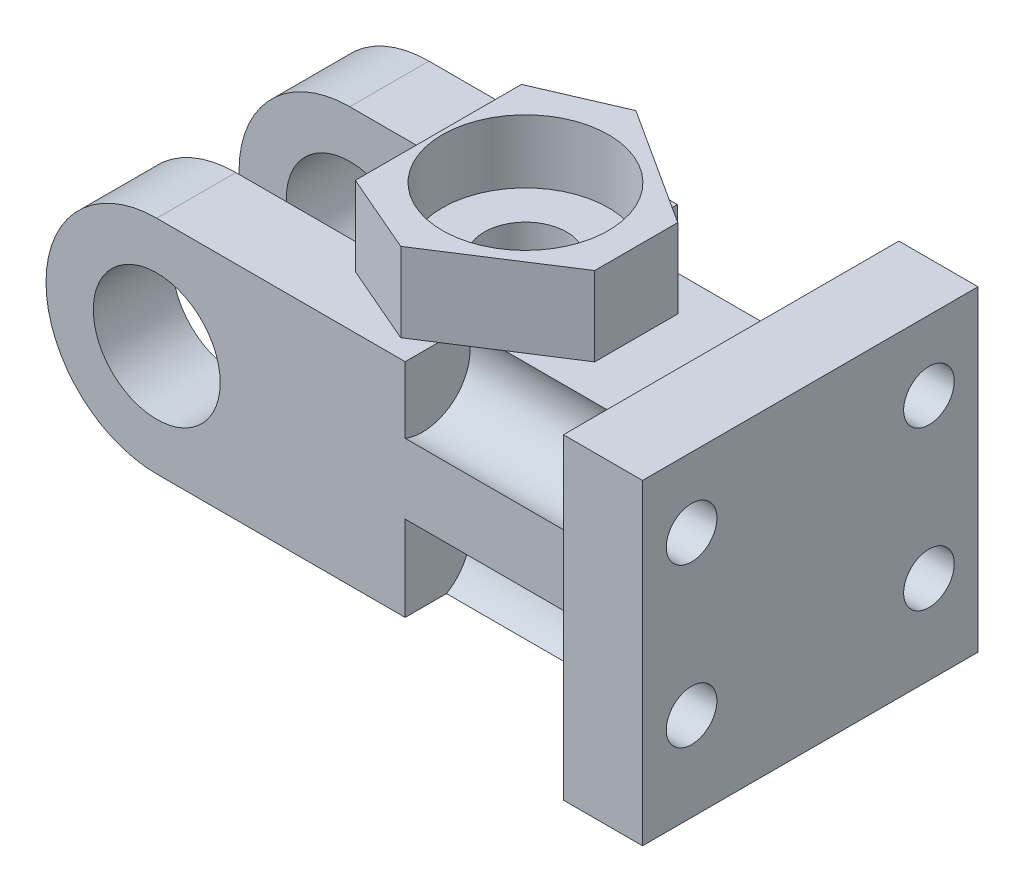
SolidWorks part; units mm, degrees
ref_plane "正面" through (0, 0, 0) normal (0, 0, 1) x (1, 0, 0)
ref_plane "平面" through (0, 0, 0) normal (0, 1, 0) x (1, 0, 0)
ref_plane "右側面" through (0, 0, 0) normal (1, 0, 0) x (0, 0, -1)
sketch "ｽｹｯﾁ1" plane through (0, 0, 0) normal (0, 0, 1) x (1, 0, 0)
  line L0 (24, 46) -> (24, 31) construction
  line L4 (24, 53) -> (51.7, 53)
  line L5 (56.7, 56) -> (56.7, 36)
  line L6 (51.7, 36) -> (56.7, 36)
  line L7 (51.7, 56) -> (51.7, 53)
  line L8 (51.7, 39) -> (51.7, 36)
  line L10 (51.7, 56) -> (56.7, 56)
  line L11 (24, 39) -> (51.7, 39)
  circle A3 centre (24, 46) radius 4.01
  circle A4 centre (53.4, 46) radius 4.05 construction
  arc A5 (24, 53) -> (24, 39) centre (24, 46) ccw
  dimension "D1" = 8.02
  dimension "D2" = 8.1
  dimension "D3" = 20
  dimension "D4" = 5
extrude "ﾎﾞｽ - 押し出し1" add sketch "ｽｹｯﾁ1" along normal blind 17.2
sketch "ｽｹｯﾁ2" plane through (0, 53, 0) normal (0, 1, 0) x (1, 0, 0)
  line L1 (17, -5) -> (33.2, -5)
  line L2 (17, -5) -> (17, -12.2)
  line L3 (17, -12.2) -> (33.2, -12.2)
  line L4 (33.2, -5) -> (33.2, -12.2)
  line L7 (38.7, 39.2569) -> (38.7, -39.2569) construction
  line L13 (51.7, 0) -> (24, 0) construction
  line L14 (51.7, -17.2) -> (24, -17.2) construction
  dimension "D1" = 5
  dimension "D2" = 5
  dimension "D3" = 16.2
extrude "ｶｯﾄ - 押し出し1" cut sketch "ｽｹｯﾁ2" against normal through all
sketch "ｽｹｯﾁ3" plane through (56.7, 0, 0) normal (1, 0, 0) x (0, 0, -1)
  line L0 (-17.2, 56) -> (0, 56) construction
  line L1 (-16.1, 51.5926) -> (-1.1, 51.5926) construction
  line L2 (-16.1, 51.5926) -> (-16.1, 41.5926) construction
  line L3 (-16.1, 41.5926) -> (-1.1, 41.5926) construction
  line L4 (-1.1, 51.5926) -> (-1.1, 41.5926) construction
  circle A0 centre (-16.1, 51.5926) radius 1.6
  circle A1 centre (-1.1, 51.5926) radius 1.6
  circle A2 centre (-16.1, 41.5926) radius 1.6
  circle A3 centre (-1.1, 41.5926) radius 1.6
  point P10 (-8.6, 56)
  point P11 (-8.6, 51.5926)
  dimension "D1" = 15
  dimension "D3" = 3.2
  dimension "D2" = 10
sketch "ｽｹｯﾁ4" plane through (56.7, 0, 0) normal (1, 0, 0) x (0, 0, -1)
  line L0 (-17.2, 36) -> (0, 36) construction
  line L1 (-17.2, 56) -> (-19.2, 56)
  line L2 (-17.2, 56) -> (-17.2, 36)
  line L3 (-17.2, 36) -> (-19.2, 36)
  line L4 (-19.2, 56) -> (-19.2, 36)
  line L5 (0, 56) -> (2, 56)
  line L6 (0, 56) -> (0, 36)
  line L7 (0, 36) -> (2, 36)
  line L8 (2, 56) -> (2, 36)
  dimension "D1" = 2
  dimension "D2" = 2
extrude "ﾎﾞｽ - 押し出し2" add sketch "ｽｹｯﾁ4" against normal up to surface (5 mm away) up to face at (51.7, 54.5, 8.6)
extrude "ｶｯﾄ - 押し出し2" cut sketch "ｽｹｯﾁ3" against normal up to surface (5 mm away) up to face at (51.7, 46, 8.6)
sketch "ｽｹｯﾁ5" plane through (56.7, 0, 0) normal (1, 0, 0) x (0, 0, -1)
  circle A0 centre (-16.1, 51.5926) radius 3
  circle A1 centre (-16.1, 41.5926) radius 3
  circle A2 centre (-1.1, 51.5926) radius 3
  circle A3 centre (-1.1, 41.5926) radius 3
  dimension "D1" = 6
extrude "ｶｯﾄ - 押し出し3" cut sketch "ｽｹｯﾁ5" against normal blind 12 from surface at -5 starting at face at (51.7, 46, 8.6)
sketch "ｽｹｯﾁ6" plane through (0, 53, 0) normal (0, 1, 0) x (1, 0, 0)
  line L0 (56.7, -19.2) -> (56.7, 2) construction
  line L1 (33.2, -3.35) -> (33.2, -13.85)
  line L3 (45.7, -11.2252) -> (45.7, -5.9748)
  line L4 (45.7, -5.9748) -> (38.2495, -1.17)
  line L5 (38.2495, -1.17) -> (33.2, -3.35)
  line L6 (33.2, -13.85) -> (38.2495, -16.03)
  line L7 (38.2495, -16.03) -> (45.7, -11.2252)
  line L8 (33.2, -12.2) -> (33.2, -5) construction
  line L9 (39.7, -17.2) -> (24, -17.2) construction
  circle A0 centre (38.7, -8.6) radius 5.5
  point P16 (45.7, -8.6)
  point P17 (33.2, -8.6)
  dimension "D1" = 18
  dimension "D2" = 11
  dimension "D3" = 7
  dimension "D4" = 8.6
  dimension "D5" = 6
  dimension "D6" = 7
  dimension "D7" = 6
  dimension "D8" = 7
  dimension "D9" = 5.5
  dimension "D10" = 10.5
extrude "ﾎﾞｽ - 押し出し7" add sketch "ｽｹｯﾁ6" along normal blind 5 contours L6 L7 L3 L4 L5 L1
sketch "ｽｹｯﾁ7" plane through (0, 58, 0) normal (0, 1, 0) x (1, 0, 0)
  line L0 (39.7, 0) -> (24, 0) construction
  line L1 (56.7, -19.2) -> (56.7, 2) construction
  circle A0 centre (38.7, -8.6) radius 5.25
  dimension "D1" = 8.6
  dimension "D3" = 10.5
  dimension "D2" = 18
extrude "ｶｯﾄ - 押し出し8" cut sketch "ｽｹｯﾁ7" against normal blind 4
sketch "ｽｹｯﾁ8" plane through (0, 54, 0) normal (0, 1, 0) x (1, 0, 0)
  circle A0 centre (38.7, -8.6) radius 2.6
  dimension "D1" = 5.2
extrude "ｶｯﾄ - 押し出し9" cut sketch "ｽｹｯﾁ8" against normal up to next
